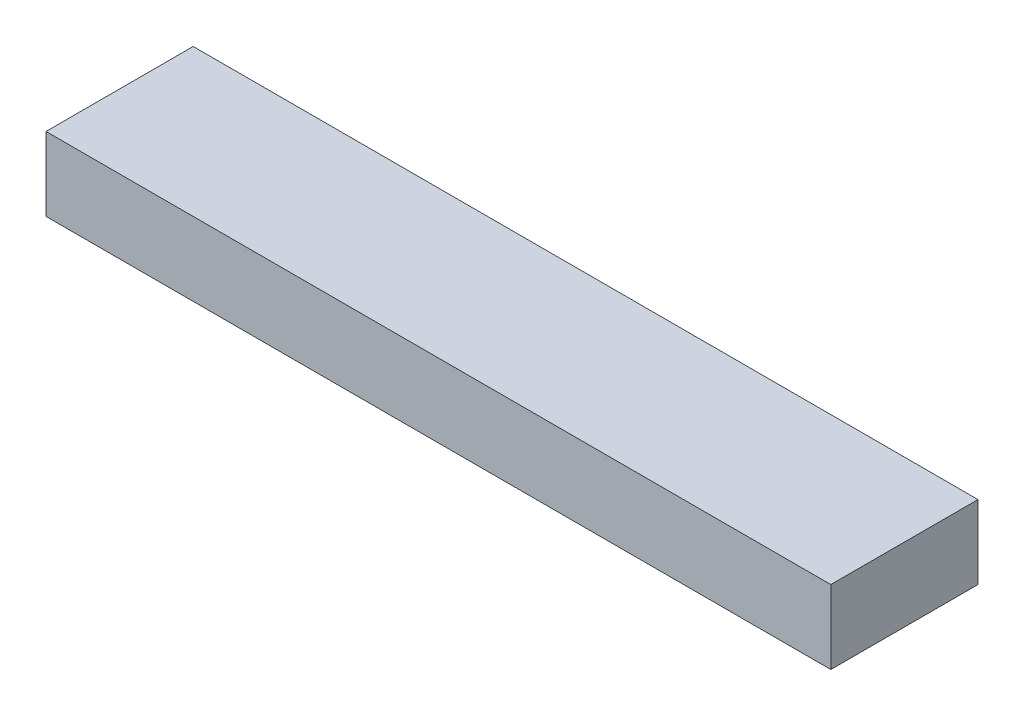
SolidWorks part; units mm, degrees
ref_plane "Front Plane" through (0, 0, 0) normal (0, 0, 1) x (1, 0, 0)
ref_plane "Top Plane" through (0, 0, 0) normal (0, 1, 0) x (1, 0, 0)
ref_plane "Right Plane" through (0, 0, 0) normal (1, 0, 0) x (0, 0, -1)
sketch "Sketch1" plane through (0, 0, 0) normal (0, 1, 0) x (1, 0, 0)
  line L1 (-270.8652, -50.8) -> (270.8652, -50.8)
  line L2 (-270.8652, -50.8) -> (-270.8652, 50.8)
  line L3 (-270.8652, 50.8) -> (270.8652, 50.8)
  line L4 (270.8652, -50.8) -> (270.8652, 50.8)
  line L5 (-270.8652, -50.8) -> (270.8652, 50.8) construction
  line L6 (-270.8652, 50.8) -> (270.8652, -50.8) construction
  point P0 (0, 0)
  dimension "D1" = 541.7304
  dimension "D2" = 101.6
extrude "Boss-Extrude1" add sketch "Sketch1" along normal blind 50.8
